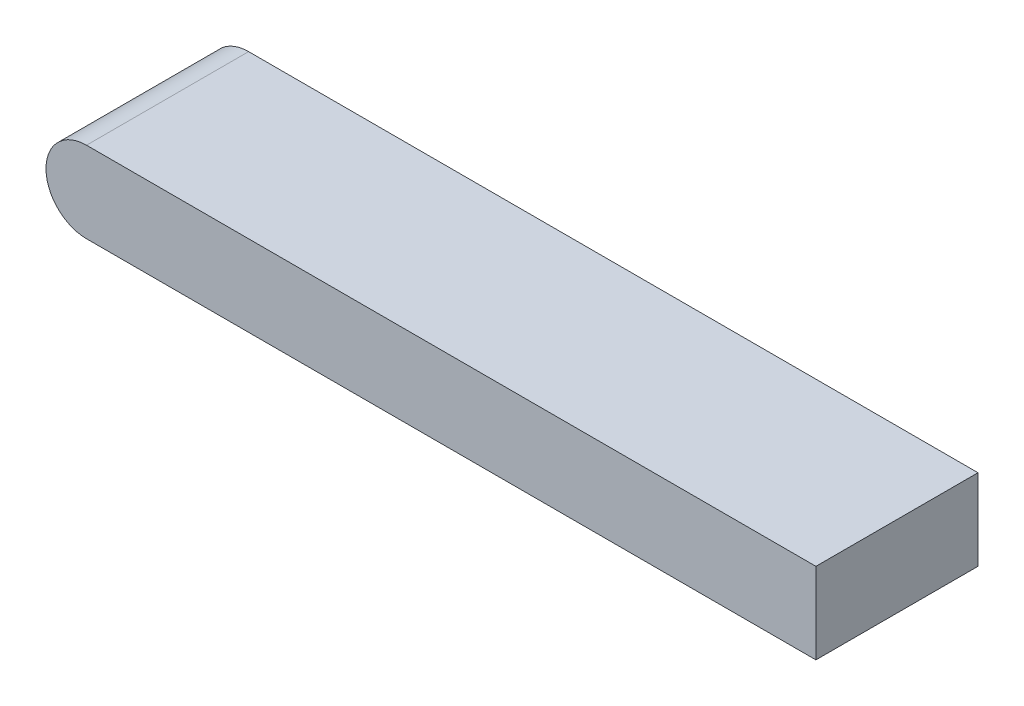
SolidWorks part; units mm, degrees
ref_plane "Front" through (0, 0, 0) normal (0, 0, 1) x (1, 0, 0)
ref_plane "Top" through (0, 0, 0) normal (0, 1, 0) x (1, 0, 0)
ref_plane "Right" through (0, 0, 0) normal (1, 0, 0) x (0, 0, -1)
sketch "草图1" plane through (0, 0, 0) normal (0, 1, 0) x (1, 0, 0)
  line L1 (-26, 4) -> (10, 4)
  line L2 (-26, 4) -> (-26, -4)
  line L3 (-26, -4) -> (10, -4)
  line L4 (10, 4) -> (10, -4)
  dimension "D1" = 8
  dimension "D2" = 36
  dimension "D3" = 10
  dimension "D4" = 4
extrude "凸台-拉伸1" add sketch "草图1" along normal blind 4
sketch "草图2" plane through (0, 0, 4) normal (0, 0, 1) x (1, 0, 0)
  line L0 (-26, 4) -> (-26, 0) construction
  circle A0 centre (-26, 2) radius 2
extrude "凸台-拉伸2" add sketch "草图2" against normal blind 8
